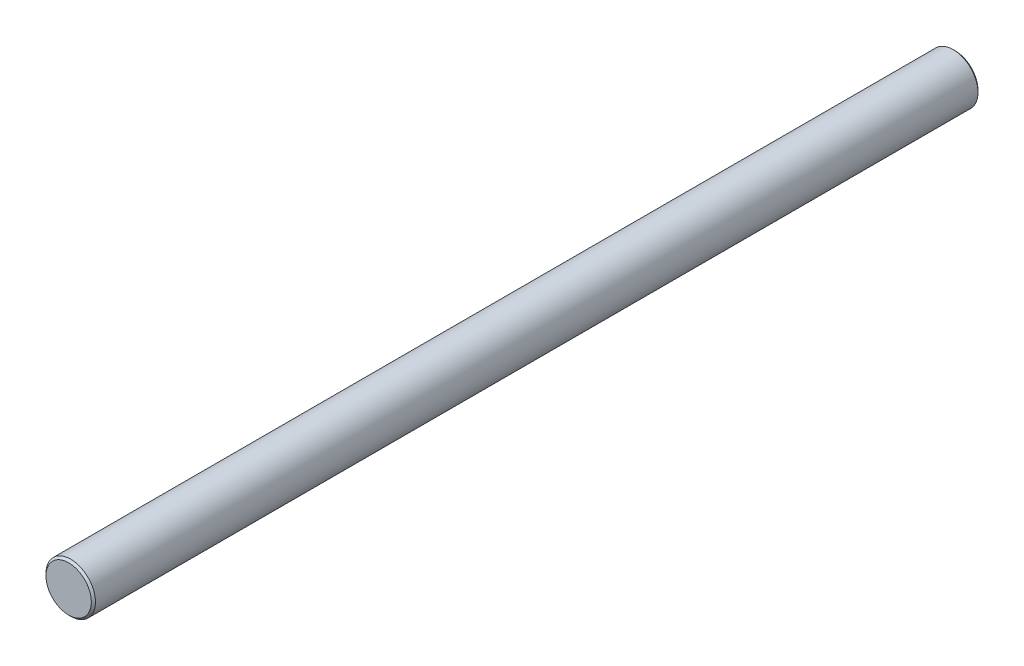
SolidWorks part; units mm, degrees
ref_plane "Front Plane" through (0, 0, 0) normal (0, 0, 1) x (1, 0, 0)
ref_plane "Top Plane" through (0, 0, 0) normal (0, 1, 0) x (1, 0, 0)
ref_plane "Right Plane" through (0, 0, 0) normal (1, 0, 0) x (0, 0, -1)
sketch "Sketch2" plane through (0, 0, 0) normal (0, 0, 1) x (1, 0, 0)
  circle A0 centre (0, 0) radius 6
  dimension "D1" = 12
extrude "Boss-Extrude1" add sketch "Sketch2" along normal mid plane 215
chamfer "Chamfer1" distance 0.5 angle 45 2 edges at (6, 0, -107.5) (6, 0, 107.5)
